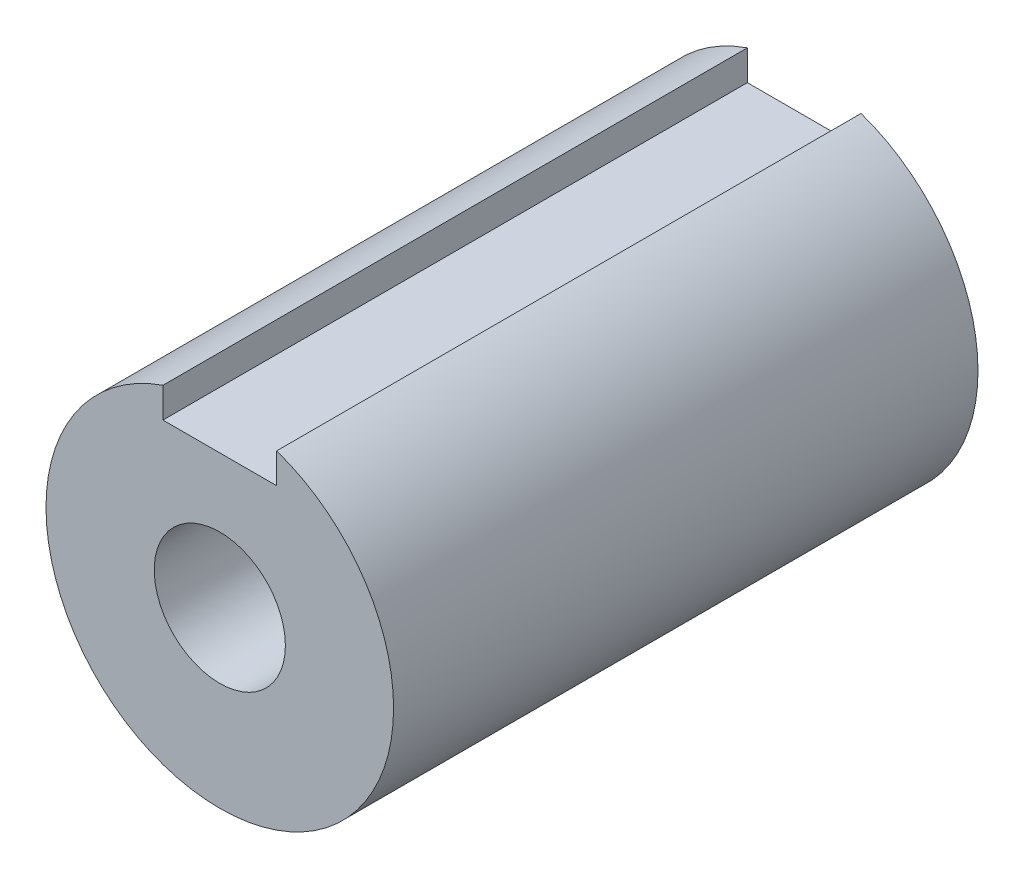
SolidWorks part; units mm, degrees
ref_plane "Plan de face" through (0, 0, 0) normal (0, 0, 1) x (1, 0, 0)
ref_plane "Plan de dessus" through (0, 0, 0) normal (0, 1, 0) x (1, 0, 0)
ref_plane "Plan de droite" through (0, 0, 0) normal (1, 0, 0) x (0, 0, -1)
sketch "Esquisse1" plane through (0, 0, 0) normal (0, 0, 1) x (1, 0, 0)
  circle A0 centre (0, 0) radius 11.925
  dimension "D1" = 23.85
extrude "Boss.-Extru.1" add sketch "Esquisse1" along normal blind 40.1
sketch "Esquisse2" plane through (0, 0, 0) normal (0, 0, 1) x (1, 0, 0)
  circle A0 centre (0, 0) radius 8.5
  dimension "D1" = 17
extrude "Enlèv. mat.-Extru.1" cut sketch "Esquisse2" along normal blind 9.77
sketch "Esquisse4" plane through (0, 0, 9.77) normal (0, 0, -1) x (-1, 0, 0)
  line L0 (-13.5783, 5.4241) -> (12.475, 5.6281) construction
  line L1 (0, 1.3948) -> (0, -8.5) construction
  line L2 (-6.4981, 5.4795) -> (6.4114, 5.5807)
  circle A0 centre (0, 0) radius 8.5 construction
  arc A1 (-6.4981, 5.4795) -> (6.4114, 5.5807) centre (0, 0) ccw
  dimension "D1" = 14.03
extrude "Enlèv. mat.-Extru.2" cut sketch "Esquisse4" against normal blind 15.5
sketch "Esquisse5" plane through (0, 0, 40.1) normal (0, 0, 1) x (1, 0, 0)
  circle A0 centre (0, 0) radius 4.5
  dimension "D1" = 9
extrude "Enlèv. mat.-Extru.3" cut sketch "Esquisse5" against normal through all
sketch "Esquisse6" plane through (0, 0, 40.1) normal (0, 0, 1) x (1, 0, 0)
  line L0 (-14.6634, 9.1996) -> (13.676, 9.1996) construction
  line L2 (0, 2.88) -> (0, 17.6586) construction
  line L3 (-3.9, 16.6712) -> (-3.9, 7.2576) construction
  line L4 (3.9, 16.9674) -> (3.9, 7.2576) construction
  line L5 (0, 0) -> (0, -11.925) construction
  line L6 (-3.9, 11.2692) -> (-3.9, 9.1996)
  line L7 (-3.9, 9.1996) -> (3.9, 9.1996)
  line L8 (3.9, 9.1996) -> (3.9, 11.2692)
  line L9 (-11.925, 0) -> (11.925, 0) construction
  circle A0 centre (0, 0) radius 11.925 construction
  arc A1 (-3.9, 11.2692) -> (3.9, 11.2692) centre (0, 0) cw
  dimension "D1" = 3.9
  dimension "D2" = 3.9
extrude "Enlèv. mat.-Extru.5" cut sketch "Esquisse6" against normal through all contours L8 A1 L6 L7
